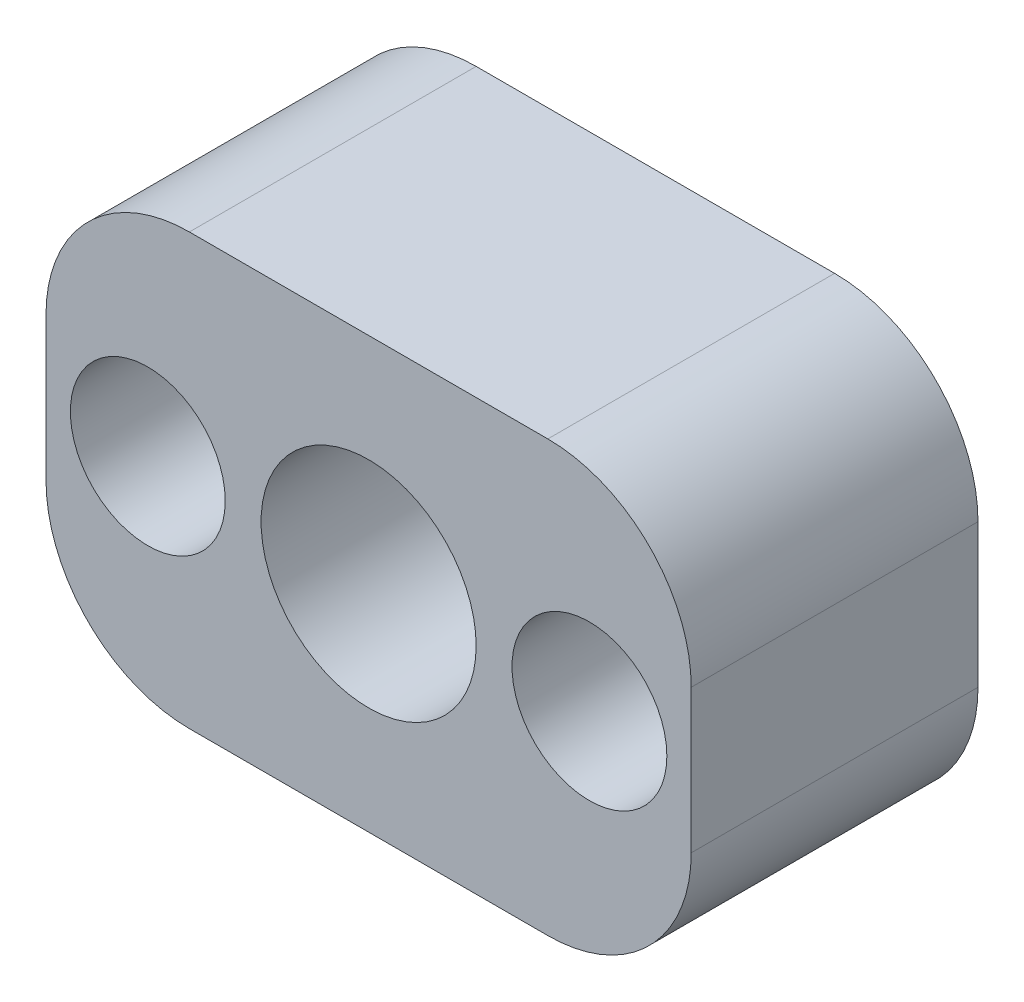
SolidWorks part; units mm, degrees
material "Copper"
ref_plane "Front Plane" through (0, 0, 0) normal (0, 0, 1) x (1, 0, 0)
ref_plane "Top Plane" through (0, 0, 0) normal (0, 1, 0) x (1, 0, 0)
ref_plane "Right Plane" through (0, 0, 0) normal (1, 0, 0) x (0, 0, -1)
sketch "Sketch1" plane through (0, 0, 0) normal (0, 0, 1) x (1, 0, 0)
  line L0 (-14.2875, 0) -> (-14.2875, -19.05)
  line L1 (0, 0) -> (-28.575, 0)
  line L2 (0, 0) -> (0, -19.05)
  line L3 (0, -19.05) -> (-28.575, -19.05)
  line L4 (-28.575, 0) -> (-28.575, -19.05)
  line L5 (-28.575, -9.525) -> (0, -9.525)
  circle A0 centre (-14.2875, -9.525) radius 4.7625
  circle A1 centre (-24.0665, -9.525) radius 1.905
  circle A2 centre (-4.5085, -9.525) radius 1.905
  dimension "D3" = 9.525
  dimension "D4" = 3.81
  dimension "D5" = 3.81
  dimension "D1" = 19.05
  dimension "D2" = 28.575
  dimension "D6" = 9.779
  dimension "D7" = 9.779
extrude "Boss-Extrude1" add sketch "Sketch1" along normal blind 12.7 contours A1 L5 A0 L0 L1 L4 | A1 L5 L4 L3 L0 A0 | A2 L5 A0 L0 L3 L2 | A2 L5 L2 L1 L0 A0
fillet "Fillet1" radius 6.35 4 edges at (-28.575, 0, 6.35) (-28.575, -19.05, 6.35) (0, -19.05, 6.35) (0, 0, 6.35)
sketch "Sketch2" plane through (0, 0, 12.7) normal (0, 0, 1) x (1, 0, 0)
  circle A0 centre (-24.0665, -9.525) radius 3.429
  circle A1 centre (-4.5085, -9.525) radius 3.429
  dimension "D1" = 6.858
  dimension "D2" = 6.858
extrude "Cut-Extrude1" cut sketch "Sketch2" against normal blind 6.35
